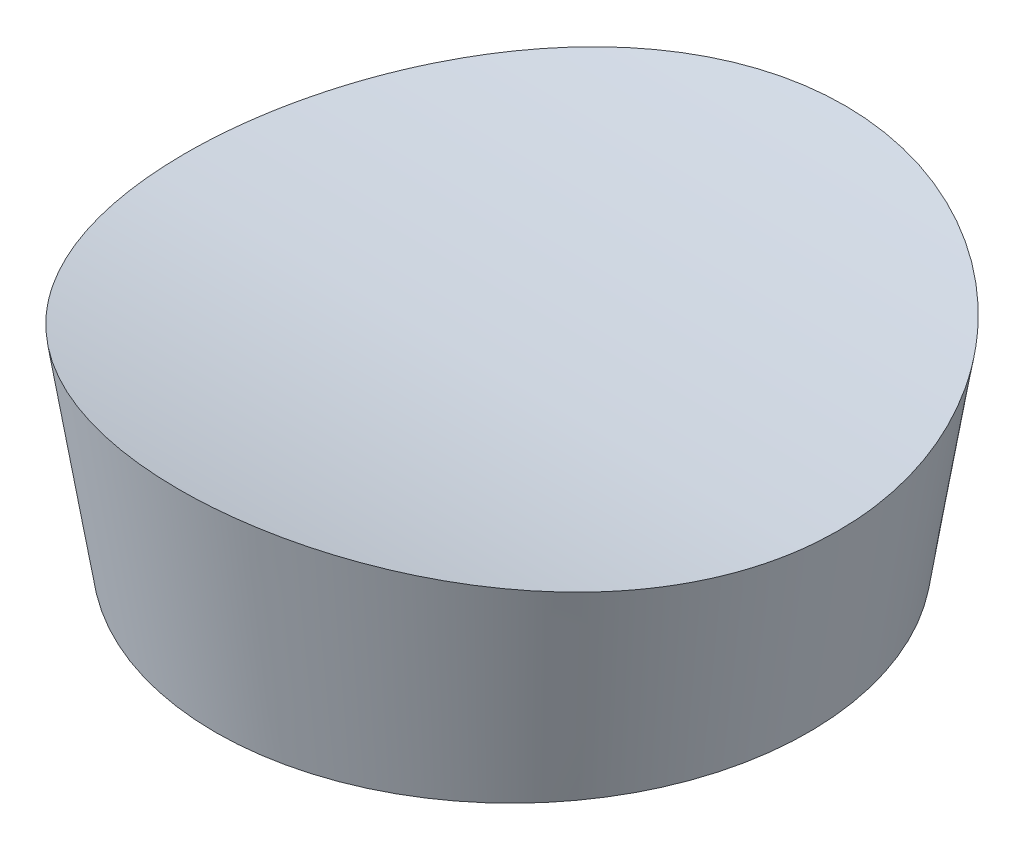
SolidWorks part; units mm, degrees
ref_plane "Front Plane" through (0, 0, 0) normal (0, 0, 1) x (1, 0, 0)
ref_plane "Top Plane" through (0, 0, 0) normal (0, 1, 0) x (1, 0, 0)
ref_plane "Right Plane" through (0, 0, 0) normal (1, 0, 0) x (0, 0, -1)
sketch "Sketch1" plane through (0, 0, 0) normal (0, 1, 0) x (1, 0, 0)
  circle A0 centre (0, 0) radius 12.5
  dimension "D1" = 25
extrude "Boss-Extrude1" add sketch "Sketch1" along normal blind 10 draft 9 draft outward yes
sketch "Sketch2" plane through (0, 0, 0) normal (0, -1, 0) x (1, 0, 0)
  circle A0 centre (0, 0) radius 9.2
  dimension "D1" = 18.4
extrude "Cut-Extrude1" cut sketch "Sketch2" against normal blind 2
sketch "Sketch3" plane through (0, 0, 0) normal (1, 0, 0) x (0, 0, -1)
  line L0 (14.0838, 10) -> (-14.0838, 10) construction
  circle A0 centre (0, 69.5) radius 61.5
  dimension "D1" = 123
  dimension "D2" = 59.5
extrude "Cut-Extrude2" cut sketch "Sketch3" against normal through all both and the other way through all
